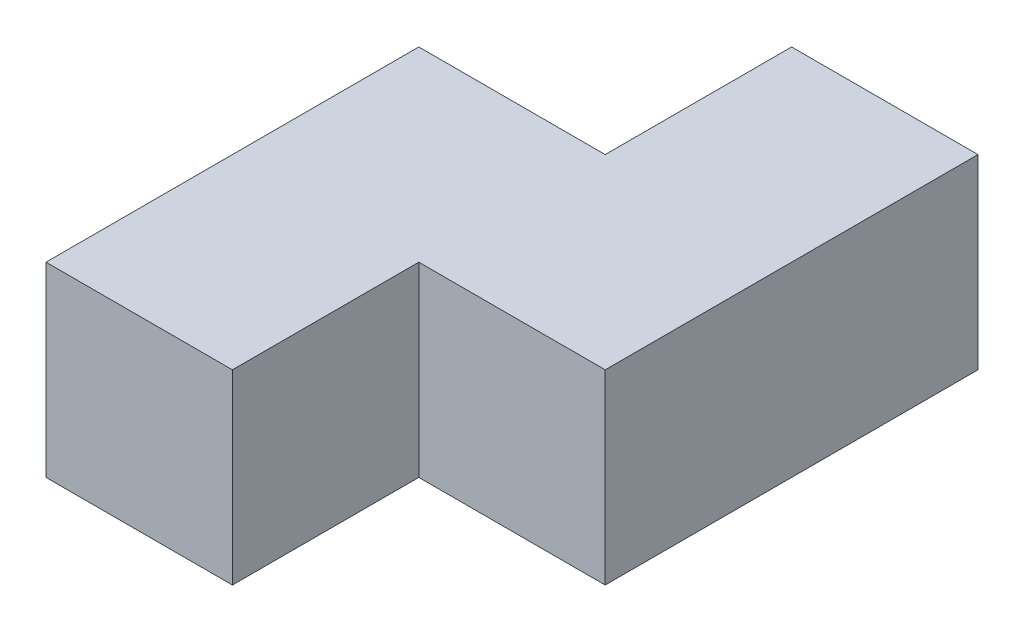
SolidWorks part; units mm, degrees
ref_plane "Front Plane" through (0, 0, 0) normal (0, 0, 1) x (1, 0, 0)
ref_plane "Top Plane" through (0, 0, 0) normal (0, 1, 0) x (1, 0, 0)
ref_plane "Right Plane" through (0, 0, 0) normal (1, 0, 0) x (0, 0, -1)
sketch "Sketch1" plane through (0, 0, 0) normal (0, 1, 0) x (1, 0, 0)
  line L0 (0, 7500) -> (0, 2500)
  line L1 (0, 2500) -> (-5000, 2500)
  line L2 (-5000, 2500) -> (-5000, -7500)
  line L3 (-5000, -7500) -> (0, -7500)
  line L4 (0, -7500) -> (0, -2500)
  line L5 (0, -2500) -> (5000, -2500)
  line L6 (5000, -2500) -> (5000, 7500)
  line L7 (5000, 7500) -> (0, 7500)
  point P11 (1788.4034, -58.3588)
  point P12 (0, 1214.9004)
  dimension "D1" = 5000
  dimension "D2" = 5000
  dimension "D3" = 5000
  dimension "D4" = 10000
  dimension "D5" = 10000
  dimension "D6" = 0
  dimension "D7" = 2500
  dimension "D8" = 5000
  dimension "D9" = 2500
extrude "Boss-Extrude1" add sketch "Sketch1" along normal blind 5000
